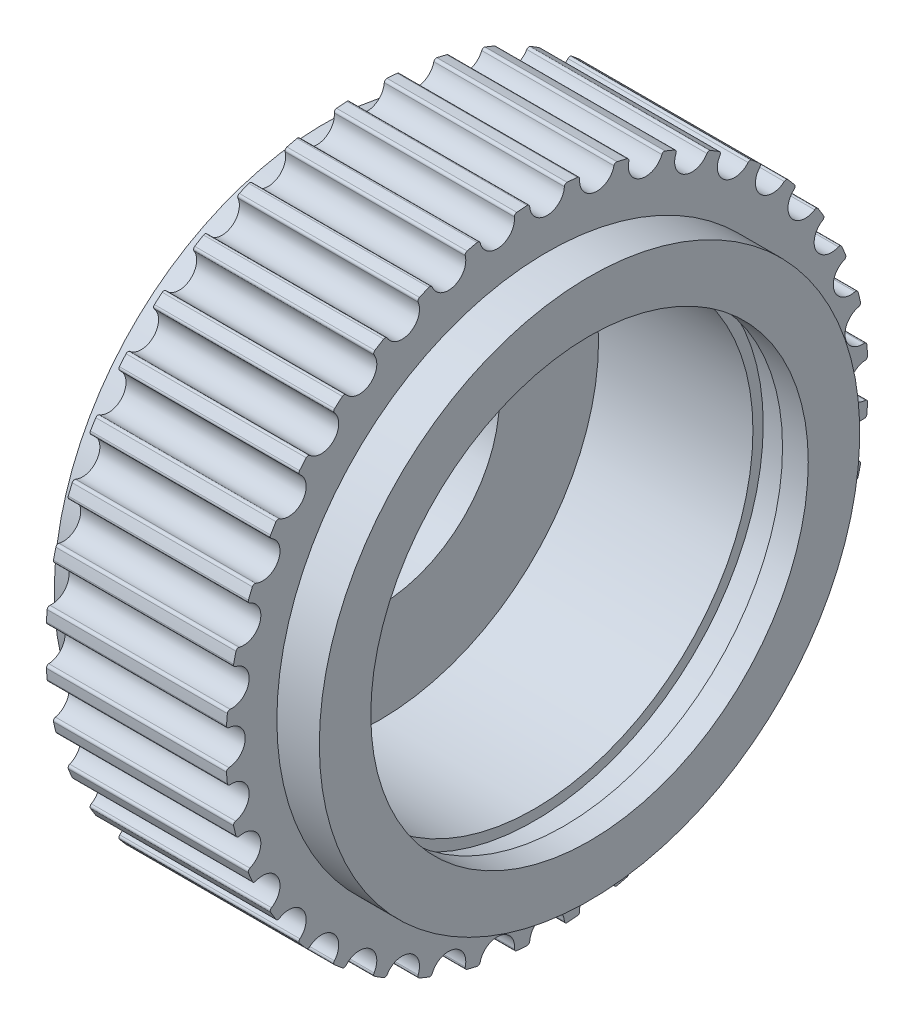
SolidWorks part; units mm, degrees
ref_plane "Front Plane" through (0, 0, 0) normal (0, 0, 1) x (1, 0, 0)
ref_plane "Top Plane" through (0, 0, 0) normal (0, 1, 0) x (1, 0, 0)
ref_plane "Right Plane" through (0, 0, 0) normal (1, 0, 0) x (0, 0, -1)
sketch "Sketch1" plane through (0, 0, 0) normal (0, 0, 1) x (1, 0, 0)
  line L0 (0, 0) -> (10.3, 0) construction
  line L1 (0, 0) -> (10.3, 0)
  line L8 (10.3, 0) -> (10.3, 10.5)
  line L9 (10.3, 10.5) -> (8.65, 10.5)
  line L10 (8.65, 10.5) -> (8.65, 12.48)
  line L11 (8.65, 12.48) -> (1.65, 12.48)
  line L12 (1.65, 12.48) -> (1.65, 10.5)
  line L13 (1.65, 10.5) -> (0, 10.5)
  line L14 (0, 10.5) -> (0, 0)
  line L15 (1.65, 12.73) -> (8.65, 12.73) construction
  line L16 (5.15, 12.48) -> (5.15, 0) construction
  dimension "O.D." = 24.96
  dimension "W" = 10.3
  dimension "A" = 7
  dimension "E" = 21
  dimension "P.D." = 25.46
  dimension "W/2" = 5.15
revolve "Revolve1" add sketch "Sketch1" angle 360 about L0
sketch "Sketch2" plane through (0, 0, 0) normal (0, 0, 1) x (1, 0, 0)
  line L0 (0, 0) -> (10.3, 0) construction
  line L1 (0, 4.65) -> (2.15, 4.65)
  line L2 (2.15, 4.65) -> (2.15, 8.5)
  line L3 (2.15, 8.5) -> (8.15, 8.5)
  line L4 (8.15, 8.5) -> (8.15, 8.9)
  line L5 (8.15, 8.9) -> (9.3, 8.9)
  line L6 (9.3, 8.9) -> (9.3, 8.5)
  line L7 (9.3, 8.5) -> (10.3, 8.5)
  line L8 (10.3, 8.5) -> (10.3, 0)
  line L10 (0, 10.5) -> (0, -10.5) construction
  line L11 (0, 0) -> (10.3, 0)
  line L14 (0, 0) -> (0, 4.65)
  line L16 (5.15, 0) -> (5.15, 8.5) construction
  dimension "MSM_6" = 9.3
  dimension "D" = 17
  dimension "W" = 10.3
  dimension "MSM_1" = 17.8
  dimension "MSM_2" = 1.15
  dimension "B" = 6
  dimension "W/2" = 5.15
  dimension "G" = 17
revolve "Cut-Revolve1" cut sketch "Sketch2" angle 360 about L0
sketch "Sketch3" [suppressed] plane through (0, 0, 0) normal (0, 0, 1) x (1, 0, 0)
  line L0 (0, 0) -> (21, 0) construction
  line L1 (0, 8.5) -> (5, 8.5)
  line L2 (5, 8.5) -> (5, 9.5)
  line L3 (5, 9.5) -> (16, 9.5)
  line L4 (16, 9.5) -> (16, 10)
  line L5 (16, 10) -> (17.15, 10)
  line L6 (17.15, 10) -> (17.15, 9.5)
  line L7 (17.15, 9.5) -> (21, 9.5)
  line L8 (21, 9.5) -> (21, 0)
  line L11 (0, 0) -> (21, 0)
  line L14 (0, 0) -> (0, 8.5)
  line L16 (10.5, 0) -> (10.5, 9.5) construction
  dimension "MSM_6" = 9.3
  dimension "D" = 17
  dimension "W" = 10.3
  dimension "MSM_1" = 17.8
  dimension "MSM_2" = 1.15
  dimension "B" = 6
  dimension "W/2" = 5.15
  dimension "G" = 17
revolve "Cut-Revolve2" [suppressed] cut sketch "Sketch3" angle 360 about L0
sketch "Sketch4" [suppressed] plane through (2, 0, 0) normal (1, 0, 0) x (0, 0, -1)
  line L0 (0, 0) -> (0, 13.945) construction
  line L2 (-0.5478, 12.8333) -> (-1, 13.9091)
  line L3 (0.5478, 12.8333) -> (1, 13.9091)
  circle A0 centre (0, 0) radius 12.845 construction
  circle A1 centre (0, 0) radius 14.345 construction
  circle A2 centre (0, 0) radius 13.945 construction
  arc A8 (-1, 13.9091) -> (1, 13.9091) centre (0, 0) cw
  arc A9 (-0.5478, 12.8333) -> (0.5478, 12.8333) centre (0, 0) cw
  circle A12 centre (0, 0) radius 13.945 construction
  dimension "MSM_7" = 0.75
  dimension "MSM_8" = 0.254
  dimension "MSM_9" = 2
  dimension "MSM_10" = 22.8
extrude "Cut-Extrude1" [suppressed] cut sketch "Sketch4" along normal through all
fillet "Fillet1" [suppressed] radius 0.2
fillet "Fillet2" [suppressed] radius 0.2
pattern_circular "CirPattern1" [suppressed] count 40 over 360
sketch "Sketch5" plane through (0, 0, 0) normal (-1, 0, 0) x (0, 0, 1)
  line L0 (0, 0) -> (0, 12.405) construction
  circle A0 centre (0, 0) radius 11.73 construction
  circle A1 centre (0, 0) radius 12.734 construction
  circle A2 centre (0, 0) radius 12.48 construction
  arc A3 (-0.6726, 12.4619) -> (0.6726, 12.4619) centre (0, 12.405) ccw
  arc A8 (-0.6726, 12.4619) -> (0.6726, 12.4619) centre (0, 0) cw
  dimension "MSM_7" = 0.75
  dimension "MSM_8" = 0.254
  dimension "O.D." = 24.96
  dimension "MSM_13" = 0.675
extrude "Cut-Extrude2" cut sketch "Sketch5" against normal through all
fillet "Fillet3" radius 0.1 2 edges at (5.15, 12.4619, -0.6726) (5.15, 12.4619, 0.6726)
pattern_circular "CirPattern2" count 40 over 360 about axis through (0, 0, 0) along (1, 0, 0) of "Cut-Extrude2", "Fillet3"
equation "\"W/2@Sketch1\" = \"W@Sketch1\" / 2"
equation "\"W/2@Sketch2\"=\"W@Sketch2\"/2"
equation "\"W/2@Sketch3\"=\"W@Sketch3\"/2"
